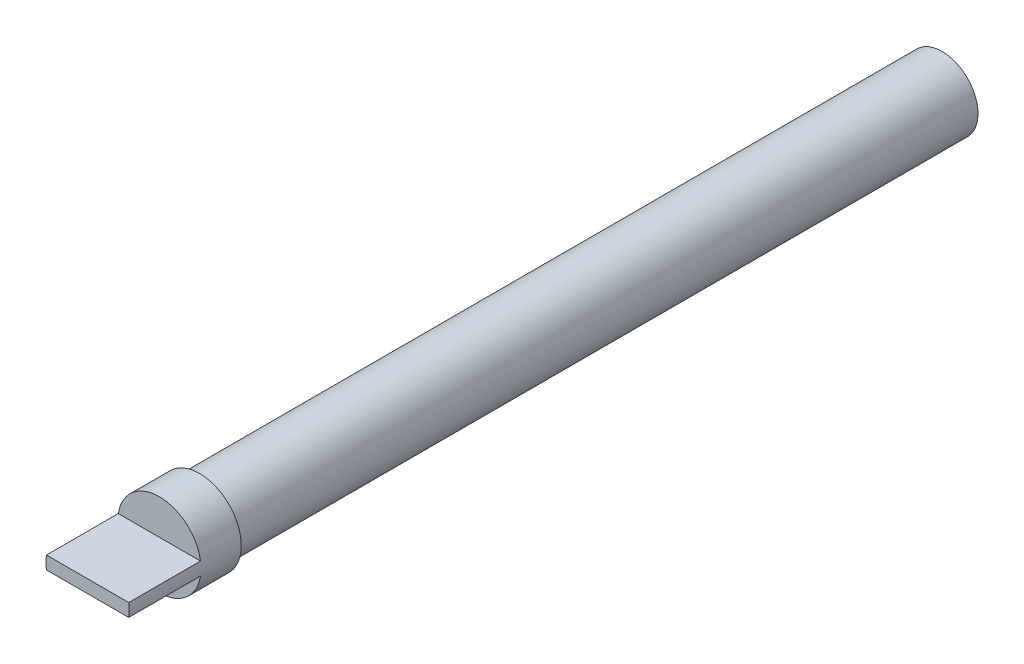
SolidWorks part; units mm, degrees
material "Mosiądz"
ref_plane "Płaszczyzna przednia" through (0, 0, 0) normal (0, 0, 1) x (1, 0, 0)
ref_plane "Płaszczyzna górna" through (0, 0, 0) normal (0, 1, 0) x (1, 0, 0)
ref_plane "Płaszczyzna prawa" through (0, 0, 0) normal (1, 0, 0) x (0, 0, -1)
sketch "Szkic1" plane through (0, 0, 0) normal (0, 0, 1) x (1, 0, 0)
  circle A0 centre (0, 0) radius 2.9
extrude "Dodanie-wyciągnięcie1" add sketch "Szkic1" along normal blind 7.8
sketch "Szkic2" plane through (0, 0, 7.8) normal (0, 0, 1) x (1, 0, 0)
  line L2 (0, -0.45) -> (2.8649, -0.45)
  line L3 (2.8649, -0.45) -> (2.8649, -2.9)
  line L4 (2.8649, -2.9) -> (-2.9, -2.9)
  line L5 (-2.9, -2.9) -> (-2.9, -0.45)
  line L6 (-2.9, -0.45) -> (0, -0.45)
  line L7 (0, 0.45) -> (2.8649, 0.45)
  line L8 (2.8649, 0.45) -> (2.8649, 2.9)
  line L9 (2.8649, 2.9) -> (-3.3056, 2.9)
  line L10 (-3.3056, 2.9) -> (-3.3056, 0.45)
  line L11 (-3.3056, 0.45) -> (0, 0.45)
  circle A0 centre (0, 0) radius 2.9 construction
extrude "Wytnij-wyciągnięcie1" cut sketch "Szkic2" against normal blind 5
sketch "Szkic3" plane through (0, 0, 0) normal (0, 0, -1) x (-1, 0, 0)
  circle A0 centre (0, 0) radius 2.5
extrude "Dodanie-wyciągnięcie2" add sketch "Szkic3" along normal blind 51.7 contours A0
hole_wizard "Otwór Ø3.5 (3.5)2" positions "Szkic 3D1" profile "Szkic7" hole size "Ø3.5" standard "ISO"
sketch3d "Szkic 3D1"
  line L0 (0, 0, -51.7) -> (0, 0, 0) construction
  point P0 (0, 0, 0)
  point P3 (2.4015, 2.5981, 0)
  point P5 (0, 0, 0)
  point P7 (0, 0, -51.7)
sketch "Szkic7" plane through (0, 0, -51.7) normal (1, 0, 0) x (0, 1, 0)
  line L0 (0, 0) -> (0, 18.0515)
  line L1 (0, 18.0515) -> (1.75, 17)
  line L2 (1.75, 17) -> (1.75, 0)
  line L5 (1.75, 0) -> (0, 0)
  line L10 (0, 18.0515) -> (-1.75, 17) construction
  line L11 (0, -6.35) -> (0, 107.95) construction
  dimension "Średnica otworu" = 3.5
  dimension "Głębokość otworu" = 17
  dimension "Kąt wiertła" = 118
